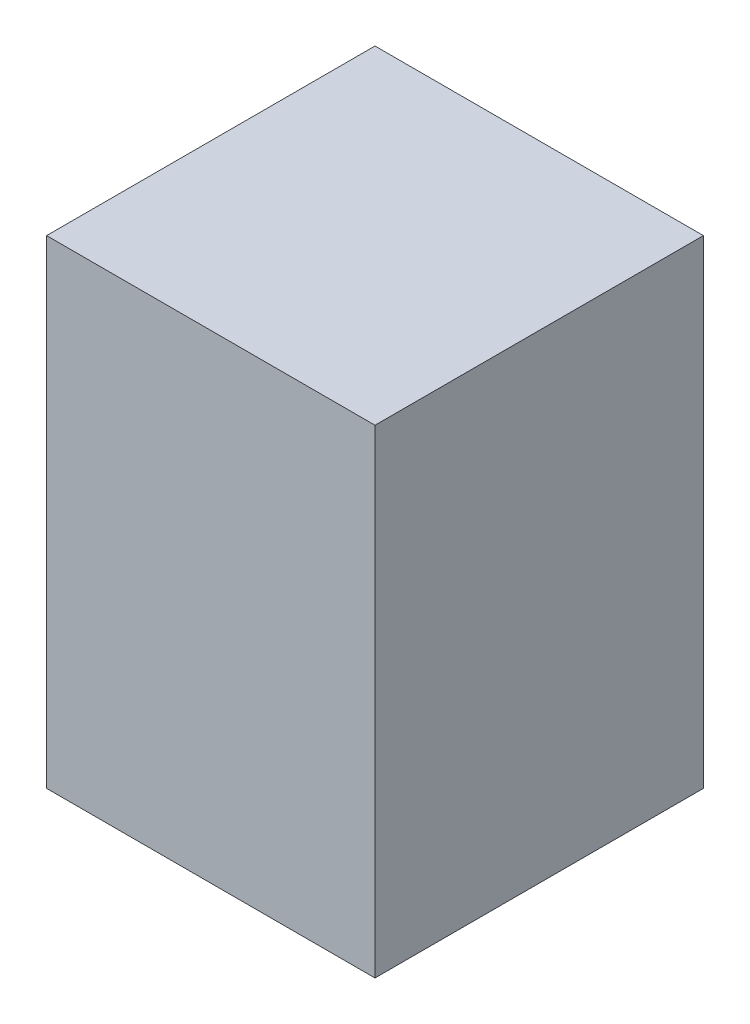
SolidWorks part; units mm, degrees
ref_plane "Front Plane" through (0, 0, 0) normal (0, 0, 1) x (1, 0, 0)
ref_plane "Top Plane" through (0, 0, 0) normal (0, 1, 0) x (1, 0, 0)
ref_plane "Right Plane" through (0, 0, 0) normal (1, 0, 0) x (0, 0, -1)
sketch "Sketch1" plane through (0, 0, 0) normal (0, 1, 0) x (1, 0, 0)
  line L1 (-171.5, -171.5) -> (171.5, -171.5)
  line L2 (-171.5, -171.5) -> (-171.5, 171.5)
  line L3 (-171.5, 171.5) -> (171.5, 171.5)
  line L4 (171.5, -171.5) -> (171.5, 171.5)
  line L5 (-171.5, -171.5) -> (171.5, 171.5) construction
  line L6 (-171.5, 171.5) -> (171.5, -171.5) construction
  point P0 (0, 0)
  dimension "D1" = 343
  dimension "D2" = 343
extrude "Boss-Extrude1" add sketch "Sketch1" along normal blind 440 and the other way blind 60
